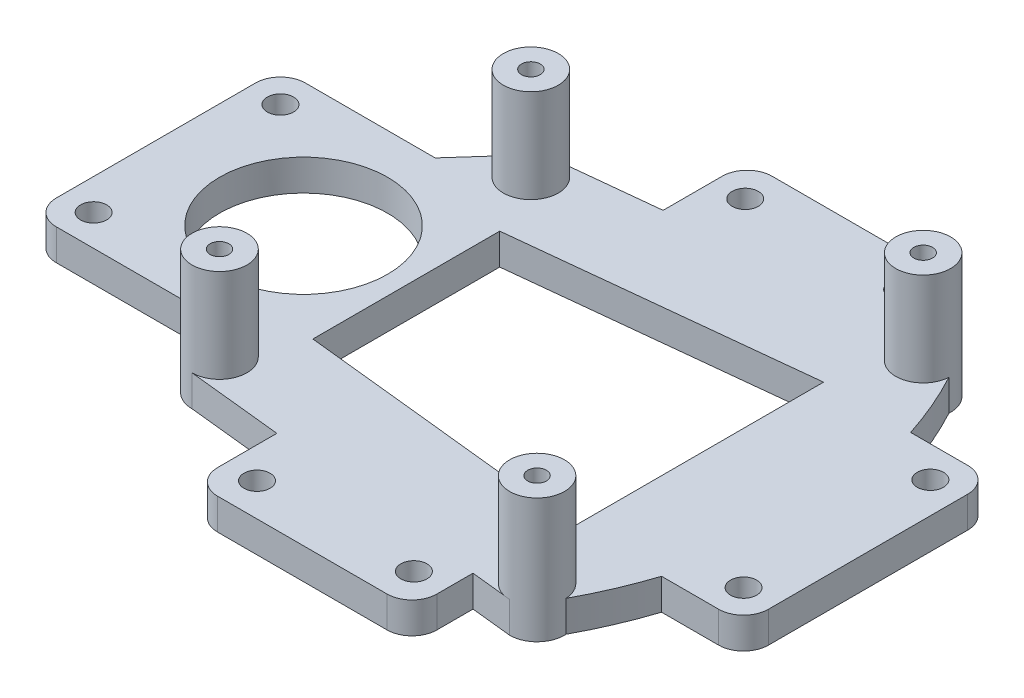
SolidWorks part; units mm, degrees
ref_plane "Front Plane" through (0, 0, 0) normal (0, 0, 1) x (1, 0, 0)
ref_plane "Top Plane" through (0, 0, 0) normal (0, 1, 0) x (1, 0, 0)
ref_plane "Right Plane" through (0, 0, 0) normal (1, 0, 0) x (0, 0, -1)
sketch "Sketch6" plane through (0, 0, 0) normal (0, 1, 0) x (1, 0, 0)
  circle A26 centre (-35.225, 25) radius 1.5
  circle A27 centre (21.775, 31) radius 1.5
  circle A28 centre (21.775, -31) radius 1.5
  circle A29 centre (-35.225, -25) radius 1.5
  circle A30 centre (-35.225, 25) radius 4.4116
  circle A31 centre (21.775, 31) radius 4.4047
  circle A36 centre (21.775, -31) radius 4.4047
  circle A39 centre (-35.225, -25) radius 4.4116
  circle A40 centre (-46.7241, 0) radius 12.5
  point P12 (0, 0)
  point P53 (33.9319, 0)
sketch "Sketch7" plane through (0, 0, 0) normal (0, 1, 0) x (1, 0, 0)
  circle A0 centre (-35.225, 25) radius 4.4116
  circle A1 centre (-35.225, 25) radius 1.5
  circle A2 centre (21.775, 31) radius 4.4047
  circle A3 centre (21.775, 31) radius 1.5
  circle A4 centre (21.775, -31) radius 4.4047
  circle A5 centre (21.775, -31) radius 1.5
  circle A6 centre (-35.225, -25) radius 1.5
  circle A7 centre (-35.225, -25) radius 4.4116
extrude "Boss-Extrude1" add sketch "Sketch7" against normal blind 15
sketch "Sketch8" plane through (0, -15, 0) normal (0, -1, 0) x (-1, 0, 0)
  circle A0 centre (35.225, -25) radius 3.5
  circle A1 centre (-21.775, -31) radius 3.5
  circle A2 centre (35.225, 25) radius 3.5
  circle A3 centre (-21.775, 31) radius 3.5
  dimension "D1" = 7
  dimension "D2" = 7
  dimension "D3" = 7
  dimension "D4" = 7
extrude "Cut-Extrude1" cut sketch "Sketch8" against normal blind 5
sketch "Sketch9" plane through (0, -15, 0) normal (0, -1, 0) x (-1, 0, 0)
  line L1 (55.5629, -8.8388) -> (38.7647, -27.6331)
  line L2 (35.225, -29.4116) -> (-21.775, -35.4047)
  line L6 (35.225, 29.4116) -> (-21.775, 35.4047)
  line L7 (55.5629, 8.8388) -> (38.7647, 27.6331)
  arc A0 (55.5629, -8.8388) -> (55.5629, 8.8388) centre (46.7241, 0) ccw
  circle A1 centre (35.225, -25) radius 4.4116 construction
  circle A2 centre (-21.775, -31) radius 4.4047 construction
  arc A3 (-26.1712, -30.7256) -> (-26.1712, 30.7256) centre (30.7713, 0) cw
  arc A4 (35.225, -29.4116) -> (38.7647, -27.6331) centre (35.225, -25) ccw
  arc A5 (-26.1712, -30.7256) -> (-20.8589, -35.3084) centre (-21.775, -31) ccw
  arc A6 (38.7647, 27.6331) -> (35.225, 29.4116) centre (35.225, 25) ccw
  arc A7 (-20.8589, 35.3084) -> (-26.1712, 30.7256) centre (-21.775, 31) ccw
  circle A13 centre (35.225, 25) radius 3.5
  arc A14 (-20.8589, 35.3084) -> (-26.1712, 30.7256) centre (-21.775, 31) ccw
  circle A15 centre (-21.775, 31) radius 3.5
  arc A16 (35.225, -29.4116) -> (38.7647, -27.6331) centre (35.225, -25) ccw
  arc A17 (-26.1712, -30.7256) -> (-20.8589, -35.3084) centre (-21.775, -31) ccw
  circle A18 centre (35.225, -25) radius 3.5
  circle A19 centre (-21.775, -31) radius 3.5
  arc A23 (38.7647, 27.6331) -> (35.225, 29.4116) centre (35.225, 25) ccw
  circle M14 centre (35.225, -25) radius 3.5
  circle M15 centre (35.225, -25) radius 4.4116
extrude "Boss-Extrude9" add sketch "Sketch9" along normal blind 5 contours L6 A7 A3 A5 L2 L1 A0 L7 A6 A19 A15 A13 M15 | M15 M14
sketch "Sketch12" plane through (0, -15, 0) normal (0, 1, 0) x (1, 0, 0)
  line L0 (0, 0) -> (0, 29.5084) construction
  line L1 (0, 0) -> (-59.2241, 0) construction
  line L3 (0, 29.5084) -> (15.1963, 29.5084)
  line L6 (15.1963, 29.5084) -> (15.1963, 44.5084)
  line L7 (0, 29.5084) -> (-15, 29.5084)
  line L11 (-20, 44.5084) -> (15.1963, 44.5084)
  line L14 (-15, 29.5084) -> (-20, 29.5084)
  line L15 (-20, 44.5084) -> (-20, 29.5084)
  line L16 (-20, 39.2003) -> (15.1963, 39.2003) construction
  line L17 (-20, -44.5084) -> (-20, -29.5084)
  line L18 (-15, -29.5084) -> (-20, -29.5084)
  line L19 (0, -29.5084) -> (-15, -29.5084)
  line L20 (0, -29.5084) -> (15.1963, -29.5084)
  line L21 (15.1963, -29.5084) -> (15.1963, -44.5084)
  line L22 (-20, -44.5084) -> (15.1963, -44.5084)
  arc A0 (-55.5629, 8.8388) -> (-55.5629, -8.8388) centre (-46.7241, 0) ccw construction
  circle A1 centre (-15, 39.2003) radius 2.1
  circle A2 centre (10.1963, 39.2003) radius 2.1
  circle A3 centre (-15, -39.2003) radius 2.1
  circle A4 centre (10.1963, -39.2003) radius 2.1
  dimension "D1" = 4.2
  dimension "D2" = 4.2
  dimension "D3" = 5
  dimension "D4" = 5
extrude "Boss-Extrude10" add sketch "Sketch12" against normal blind 5
fillet "Fillet3" radius 4 4 edges at (15.1963, -17.5, -44.5084) (-20, -17.5, -44.5084) (15.1963, -17.5, 44.5084) (-20, -17.5, 44.5084)
sketch "Sketch13" plane through (0, -15, 0) normal (0, 1, 0) x (1, 0, 0)
  line L0 (-50.4357, 0) -> (33.9319, 0) construction
  line L1 (-50.4357, -10) -> (-70.4357, -10)
  line L3 (-50.4357, -10) -> (-50.4357, 10)
  line L4 (-50.4357, 10) -> (-70.4357, 10)
  line L5 (-70.4357, -10) -> (-70.4357, 10)
  arc A1 (26.1712, -30.7256) -> (26.1712, 30.7256) centre (-30.7713, 0) ccw construction
  circle A2 centre (-65.4357, 5) radius 2.3833
  circle A3 centre (-65.4357, -5) radius 2.3833
  dimension "D2" = 5
  dimension "D3" = 5
  dimension "D1" = 20
extrude "Boss-Extrude11" add sketch "Sketch13" against normal blind 5
fillet "Fillet4" radius 4 2 edges at (-70.4357, -17.5, 10) (-70.4357, -17.5, -10)
sketch "Sketch14" plane through (0, -15, 0) normal (0, 1, 0) x (1, 0, 0)
  line L0 (33.9319, 0) -> (4.4107, 0) construction
  line L2 (23.9319, -20) -> (43.9319, -20)
  line L3 (23.9319, -20) -> (23.9319, 20)
  line L4 (23.9319, 20) -> (43.9319, 20)
  line L5 (43.9319, -20) -> (43.9319, 20)
  line L6 (23.9319, -20) -> (43.9319, 20) construction
  line L7 (23.9319, 20) -> (43.9319, -20) construction
  arc A0 (26.1712, -30.7256) -> (26.1712, 30.7256) centre (-30.7713, 0) ccw construction
  circle A1 centre (38.9319, 15) radius 2.1
  circle A2 centre (38.9319, -15) radius 2.1
  circle A3 centre (-65.4357, 5) radius 2.3833
  circle A4 centre (-65.4357, -5) radius 2.3833
  circle A5 centre (-65.4357, -5) radius 2.1
  circle A6 centre (-65.4357, 5) radius 2.1
  dimension "D3" = 4.2
  dimension "D4" = 4.2
  dimension "D5" = 4.2
  dimension "D6" = 4.2
  dimension "D7" = 5
  dimension "D8" = 5
  dimension "D9" = 5
  dimension "D10" = 5
  dimension "D1" = 20
  dimension "D2" = 40
extrude "Boss-Extrude12" add sketch "Sketch14" against normal blind 5
fillet "Fillet5" radius 4 2 edges at (43.9319, -17.5, -20) (43.9319, -17.5, 20)
sketch "Sketch15" plane through (0, -15, 0) normal (0, 1, 0) x (1, 0, 0)
  line L0 (-70.4357, 0) -> (43.9319, 0) construction
  line L1 (-70.4357, 6) -> (-70.4357, -6) construction
  line L2 (43.9319, -16) -> (43.9319, 16) construction
  line L3 (-38.6147, -20) -> (-70.4354, -20)
  line L4 (39.9319, 20) -> (30.7633, 20) construction
  line L6 (-38.6147, -20) -> (-38.6147, 20)
  line L7 (-38.6147, 20) -> (-70.4354, 20)
  line L8 (-70.4354, -20) -> (-70.4354, 20)
  line L9 (-65.4357, 5) -> (-65.4357, 15) construction
  line L10 (38.9319, 15) -> (-70.4354, 15) construction
  circle A0 centre (-65.4357, 15) radius 2.1
  circle A1 centre (-65.4357, -15) radius 2.1
  point P7 (-38.6147, 0)
  point P8 (-54.525, 0)
  point P14 (-70.4354, 0)
  dimension "D2" = 4.2
  dimension "D1" = 0
extrude "Boss-Extrude13" add sketch "Sketch15" against normal blind 5
fillet "Fillet6" radius 4 2 edges at (-70.4354, -17.5, 20) (-70.4354, -17.5, -20)
sketch "Sketch16" plane through (0, -20, 0) normal (0, -1, 0) x (-1, 0, 0)
  circle A0 centre (-21.775, -31) radius 3.5
  circle A1 centre (-21.775, 31) radius 3.5
  circle A2 centre (35.225, 25) radius 3.5
  circle A3 centre (35.225, -25) radius 3.5
  circle A4 centre (35.225, -25) radius 1.5
  circle A5 centre (-21.775, -31) radius 1.5
  circle A6 centre (-21.775, 31) radius 1.5
  circle A7 centre (35.225, 25) radius 1.5
extrude "Boss-Extrude14" add sketch "Sketch16" against normal blind 15
sketch "Sketch17" plane through (0, -15, 0) normal (0, 1, 0) x (1, 0, 0)
  line L4 (-30.225, 15) -> (16.775, 20)
  line L5 (16.775, 20) -> (16.775, -20)
  line L7 (-30.225, -15) -> (-30.225, 15)
  line L11 (-30.225, -15) -> (16.775, -20)
  point P31 (16.775, 0)
  point P32 (-30.225, 0)
  dimension "D3" = 15
  dimension "D6" = 20
extrude "Cut-Extrude3" cut sketch "Sketch17" against normal blind 15
sketch "Sketch18" plane through (0, 0, 0) normal (0, 1, 0) x (1, 0, 0)
  line L0 (-35.225, 25) -> (-35.225, -25) construction
  line L1 (-70.4357, 0) -> (43.9319, 0) construction
  line L2 (-70.4357, 6) -> (-70.4357, -6) construction
  line L3 (43.9319, -16) -> (43.9319, 16) construction
  circle A0 centre (-46.725, 0) radius 13.5
  dimension "D1" = 27
  dimension "D2" = 11.5
extrude "Cut-Extrude6" cut sketch "Sketch18" against normal through all
